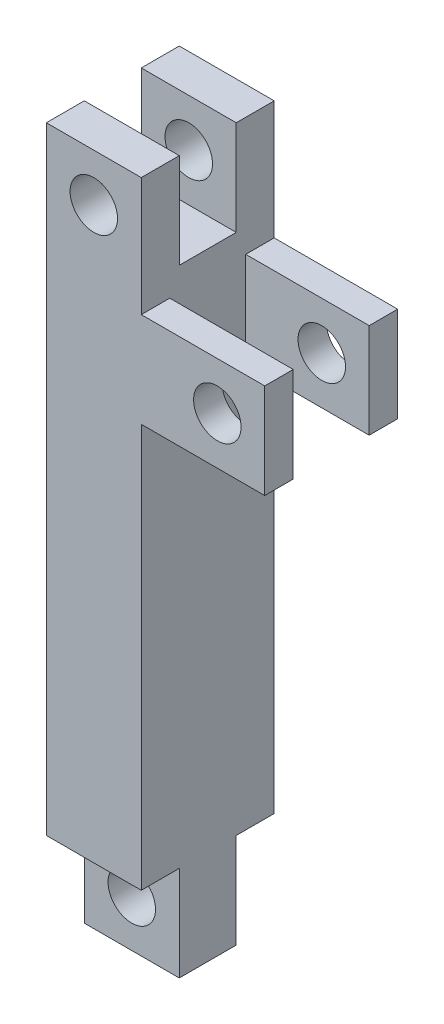
SolidWorks part; units mm, degrees
material "PEN"
ref_plane "前视基准面" through (0, 0, 0) normal (0, 0, 1) x (1, 0, 0)
ref_plane "上视基准面" through (0, 0, 0) normal (0, 1, 0) x (1, 0, 0)
ref_plane "右视基准面" through (0, 0, 0) normal (1, 0, 0) x (0, 0, -1)
sketch "草图1" plane through (0, 0, 0) normal (0, 1, 0) x (1, 0, 0)
  line L7 (5, 7) -> (-5, 7)
  line L8 (5, 7) -> (5, -7)
  line L9 (5, -7) -> (-5, -7)
  line L10 (-5, 7) -> (-5, -7)
  line L11 (5, 7) -> (-5, -7) construction
  line L12 (5, -7) -> (-5, 7) construction
  point P4 (2.5, 3.5)
extrude "凸台-拉伸1" add sketch "草图1" along normal mid plane 65
sketch "草图7" plane through (0, 0, 0) normal (0, 0, 1) x (1, 0, 0)
  line L13 (5, 32.5) -> (5, -32.5) construction
  line L16 (5, 10) -> (18, 10)
  line L17 (5, 10) -> (5, 20)
  line L18 (5, 20) -> (18, 20)
  line L19 (18, 10) -> (18, 20)
  line L20 (5, 10) -> (18, 20) construction
  line L21 (5, 20) -> (18, 10) construction
  point P8 (11.5, 15)
extrude "凸台-拉伸3" add sketch "草图7" along normal mid plane 14
sketch "草图8" plane through (0, 0, 0) normal (0, 0, 1) x (1, 0, 0)
  line L16 (5, 20) -> (18, 20)
  line L17 (5, 20) -> (5, 10)
  line L18 (5, 10) -> (18, 10)
  line L19 (18, 20) -> (18, 10)
  line L20 (5, 20) -> (18, 10) construction
  line L21 (5, 10) -> (18, 20) construction
  point P5 (11.5, 15)
extrude "切除-拉伸3" cut sketch "草图8" against normal mid plane 8
sketch "草图10" plane through (0, 0, 0) normal (0, 0, 1) x (1, 0, 0)
  circle A2 centre (13.0055, 15) radius 2.5
extrude "切除-拉伸4" cut sketch "草图10" against normal through all both and the other way through all
sketch "草图14" plane through (0, 0, 0) normal (0, 0, 1) x (1, 0, 0)
  line L0 (5, 32.5) -> (5, 20) construction
  line L1 (-5, 32.5) -> (5, 32.5)
  line L2 (-5, 32.5) -> (-5, 22.5)
  line L3 (-5, 22.5) -> (5, 22.5)
  line L4 (5, 32.5) -> (5, 22.5)
  line L5 (-5, 32.5) -> (5, 22.5) construction
  line L6 (-5, 22.5) -> (5, 32.5) construction
  point P5 (0, 27.5)
extrude "切除-拉伸8" cut sketch "草图14" against normal mid plane 6
sketch "草图15" plane through (0, 0, 0) normal (0, 0, 1) x (1, 0, 0)
  line L9 (5, -32.5) -> (-5, -32.5)
  line L10 (5, -32.5) -> (5, -42.5)
  line L11 (5, -42.5) -> (-5, -42.5)
  line L12 (-5, -32.5) -> (-5, -42.5)
  line L13 (5, -32.5) -> (-5, -42.5) construction
  line L14 (5, -42.5) -> (-5, -32.5) construction
  point P4 (0, -37.5)
extrude "凸台-拉伸4" add sketch "草图15" along normal mid plane 6
sketch "草图16" plane through (0, 0, 0) normal (0, 0, 1) x (1, 0, 0)
  circle A1 centre (0, 27.5) radius 2.5
  point P0 (0, 0)
extrude "切除-拉伸9" cut sketch "草图16" against normal through all both and the other way through all
sketch "草图17" plane through (0, 0, 0) normal (0, 0, 1) x (1, 0, 0)
  circle A1 centre (0, -37.5) radius 2.5
extrude "切除-拉伸10" cut sketch "草图17" against normal through all both and the other way through all
sketch "草图19" plane through (5, 0, 0) normal (1, 0, 0) x (0, 0, -1)
  line L0 (-7, 10) -> (-7, -32.5) construction
  line L1 (-7, 0) -> (7, 0)
  line L2 (-7, 0) -> (-7, -10)
  line L3 (-7, -10) -> (7, -10)
  line L4 (7, 0) -> (7, -10)
  line L5 (-7, 0) -> (7, -10) construction
  line L6 (-7, -10) -> (7, 0) construction
  line L7 (7, 10) -> (7, -32.5) construction
  point P4 (0, -5)
